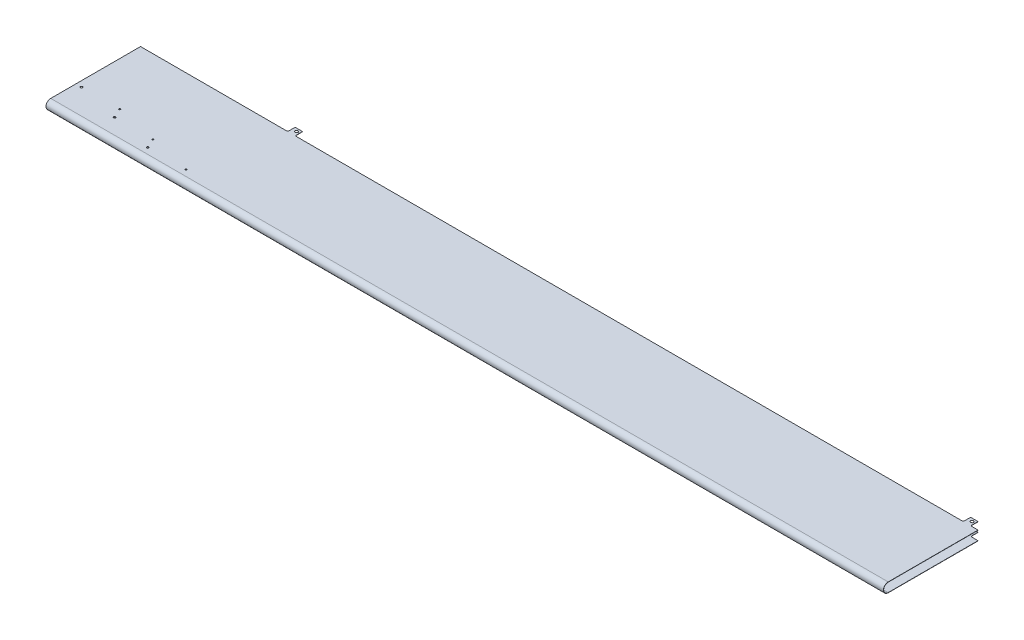
SolidWorks part; units mm, degrees
material "Kapton"
ref_plane "Front Plane" through (0, 0, 0) normal (0, 0, 1) x (1, 0, 0)
ref_plane "Top Plane" through (0, 0, 0) normal (0, 1, 0) x (1, 0, 0)
ref_plane "Right Plane" through (0, 0, 0) normal (1, 0, 0) x (0, 0, -1)
sketch "Sketch1" plane through (0, 0, 0) normal (1, 0, 0) x (0, 0, -1)
  line L0 (0, 0) -> (-61, 0)
  line L1 (-61, -6.4251) -> (0, -6.4251)
  line L2 (0, 0) -> (5, 0)
  line L3 (0, -6.4251) -> (5, -6.4251)
  line L4 (0, 0) -> (0, -6.4251) construction
  line L5 (5, -0.1626) -> (-61, -0.1626)
  line L6 (5, -6.2626) -> (-61, -6.2626)
  line L9 (5, 0) -> (5, -6.4251) construction
  line L10 (5, 0) -> (5, -0.1626)
  line L11 (5, -6.2626) -> (5, -6.4251)
  arc A0 (-61, 0) -> (-61, -6.4251) centre (-61, -3.2126) ccw
  arc A1 (-61, -0.1626) -> (-61, -6.2626) centre (-61, -3.2126) ccw
  point P5 (0, -0.1626)
  point P10 (-60.9777, -0.1626)
  point P12 (-60.9777, -6.2626)
  point P13 (0, -6.2626)
  dimension "D4" = 0.1626
  dimension "D6" = 0.1626
  dimension "D7" = 3.2126
  dimension "D8" = 0.1626
  dimension "D2" = 61
  dimension "D3" = 5
  dimension "D5" = 61
  dimension "D1" = 6.1
extrude "Boss-Extrude1" add sketch "Sketch1" against normal blind 563.8 and the other way blind 5
sketch "Sketch2" plane through (0, 0, 0) normal (0, 1, 0) x (1, 0, 0)
  line L0 (5, 0) -> (1, 0)
  line L1 (5, 5) -> (5, -61) construction
  line L2 (0, 1) -> (0, 5)
  line L3 (-563.8, 5) -> (5, 5) construction
  line L4 (0, 5) -> (-5, 5)
  line L5 (-5, 5) -> (-5, 1)
  line L6 (-6, 0) -> (-457.8, 0)
  line L7 (-458.8, 1) -> (-458.8, 5)
  line L8 (-458.8, 5) -> (-463.8, 5)
  line L9 (-463.8, 5) -> (-463.8, 1)
  line L10 (-464.8, 0) -> (-563.8, 0)
  line L11 (-563.8, 5) -> (-563.8, -61) construction
  line L12 (-563.8, 0) -> (-563.8, 10)
  line L13 (-563.8, 10) -> (5, 10)
  line L14 (5, 10) -> (5, 0)
  arc A0 (-464.8, 0) -> (-463.8, 1) centre (-464.8, 1) ccw
  arc A1 (-457.8, 0) -> (-458.8, 1) centre (-457.8, 1) cw
  arc A2 (-6, 0) -> (-5, 1) centre (-6, 1) ccw
  arc A3 (0, 1) -> (1, 0) centre (1, 1) ccw
  point P22 (-458.8, 0)
  point P25 (-5, 0)
  point P28 (0, 0)
  dimension "D7" = 1
  dimension "D1" = 5
  dimension "D2" = 5
  dimension "D3" = 10
  dimension "D4" = 453.8
  dimension "D5" = 5
  dimension "D6" = 5
extrude "Cut-Extrude1" cut sketch "Sketch2" against normal through all
sketch "Sketch3" plane through (-563.8, 0, 0) normal (-1, 0, 0) x (0, 0, 1)
  line L2 (61, -0.2311) -> (0, -0.2311)
  line L3 (0, -6.194) -> (61, -6.194)
  line L4 (0, -0.2311) -> (0, 0)
  line L5 (0, 0) -> (61, 0)
  line L6 (61, -6.4251) -> (0, -6.4251)
  line L7 (0, -6.4251) -> (0, -6.194)
  line L8 (61, -0.2311) -> (61, 0) construction
  line L9 (61, -6.194) -> (61, -6.4251) construction
  line L10 (0, 0) -> (61, 0) construction
  line L11 (61, -6.4251) -> (0, -6.4251) construction
  arc A0 (61, -6.4251) -> (61, 0) centre (61, -3.2126) ccw construction
  arc A1 (61, -0.2311) -> (61, -6.194) centre (61, -3.2126) cw
  arc A2 (61, 0) -> (61, -6.4251) centre (61, -3.2126) cw
  arc A5 (61, -0.2311) -> (61, -6.194) centre (61, -3.2126) cw construction
  dimension "D3" = 0.2311
  dimension "D1" = 0.2311
  dimension "D2" = 0.2311
extrude "Boss-Extrude2" add sketch "Sketch3" against normal blind 91.3
sketch "Sketch4" plane through (0, 0, 0) normal (0, 1, 0) x (1, 0, 0)
  line L0 (-560.001, -43.918) -> (-563.8, -43.918) construction
  line L1 (-563.8, 0) -> (-563.8, -61) construction
  line L2 (-560.001, -43.918) -> (-534.001, -43.918) construction
  line L6 (-531.001, -50.418) -> (-531.001, -56.918) construction
  line L7 (-531.001, -56.918) -> (-502.001, -56.918) construction
  line L8 (-531.001, -50.418) -> (-505.001, -50.418) construction
  line L10 (-502.001, -56.918) -> (-476.001, -56.918) construction
  line L11 (-560.001, -43.918) -> (-560.001, 0) construction
  line L12 (-563.8, 0) -> (-464.8, 0) construction
  line L13 (-560.001, -43.918) -> (-560.001, -50.418) construction
  line L14 (-560.001, -50.418) -> (-531.001, -50.418) construction
  circle A0 centre (-560.001, -43.918) radius 0.69
  circle A1 centre (-534.001, -43.918) radius 0.51
  circle A2 centre (-531.001, -50.418) radius 0.69
  circle A3 centre (-505.001, -50.418) radius 0.51
  circle A4 centre (-502.001, -56.918) radius 0.69
  circle A5 centre (-476.001, -56.918) radius 0.51
  dimension "D10" = 1.38
  dimension "D11" = 1.02
  dimension "D1" = 3.799
  dimension "D2" = 26
  dimension "D3" = 29
  dimension "D4" = 26
  dimension "D5" = 29
  dimension "D6" = 26
  dimension "D7" = 43.918
  dimension "D8" = 6.5
  dimension "D9" = 6.5
extrude "Cut-Extrude2" cut sketch "Sketch4" against normal blind 2
sketch "Sketch5" plane through (0, 0, 0) normal (0, 1, 0) x (1, 0, 0)
  line L0 (-458.8, 5) -> (-458.8, 1) construction
  line L1 (-458.8, 5) -> (-463.8, 5) construction
  line L2 (0, 5) -> (0, 1) construction
  circle A0 centre (-460.8, 2.99) radius 1
  circle A1 centre (-2, 2.99) radius 1
  dimension "D1" = 2
  dimension "D2" = 2.01
  dimension "D3" = 2
extrude "Cut-Extrude3" cut sketch "Sketch5" against normal through all
